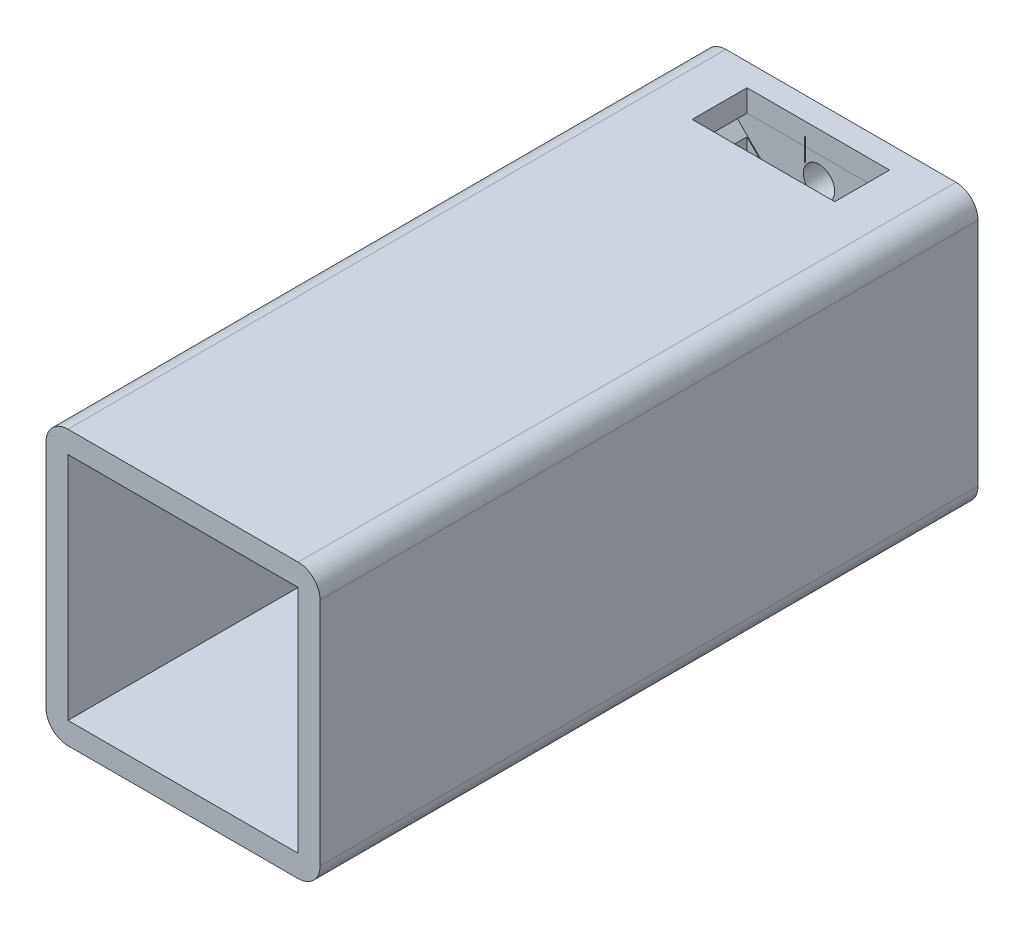
SolidWorks part; units mm, degrees
ref_plane "Front Plane" through (0, 0, 0) normal (0, 0, 1) x (1, 0, 0)
ref_plane "Top Plane" through (0, 0, 0) normal (0, 1, 0) x (1, 0, 0)
ref_plane "Right Plane" through (0, 0, 0) normal (1, 0, 0) x (0, 0, -1)
sketch "Sketch1" plane through (0, 0, 0) normal (0, 0, 1) x (1, 0, 0)
  line L1 (-12.5, -12.5) -> (12.5, -12.5)
  line L2 (-12.5, -12.5) -> (-12.5, 12.5)
  line L3 (-12.5, 12.5) -> (12.5, 12.5)
  line L4 (12.5, -12.5) -> (12.5, 12.5)
  line L5 (-12.5, -12.5) -> (12.5, 12.5) construction
  line L6 (-12.5, 12.5) -> (12.5, -12.5) construction
  point P0 (0, 0)
  dimension "D1" = 25
sketch "Sketch2" plane through (0, 0, 0) normal (0, 0, 1) x (1, 0, 0)
  line L5 (-12.5, -12.5) -> (12.5, 12.5) construction
  line L6 (-12.5, 12.5) -> (12.5, -12.5) construction
  circle A0 centre (0, 0) radius 2.5
  circle A1 centre (8.25, 0) radius 1.425
  circle A2 centre (0, -8.25) radius 1.425
  circle A3 centre (-8.25, 0) radius 1.425
  circle A4 centre (0, 8.25) radius 1.425
  point P0 (0, 0)
  dimension "D2" = 4
  dimension "D1" = 25
extrude "Boss-Extrude1" add sketch "Sketch1" along normal blind 60
shell "Shell1" thickness 2
extrude "Cut-Extrude4" cut sketch "Sketch2" along normal blind 2
sketch "Sketch4" plane through (0, 0, 2) normal (0, 0, 1) x (1, 0, 0)
  line L0 (0, 0) -> (-8.2, 0)
  line L1 (-5.7033, -6) -> (4.2967, -6)
  line L3 (-5.7033, 6) -> (4.2967, 6)
  line L5 (-5.7033, -6) -> (4.2967, 6) construction
  line L6 (-5.7033, 6) -> (4.2967, -6) construction
  line L7 (0, 0) -> (8.2, 0)
  line L8 (0, 0) -> (0, 6)
  line L9 (0, 0) -> (0, -6)
  line L11 (-10.5, 8.3787) -> (8.3787, -10.5)
  line L12 (-10.5, -10.5) -> (10.5, -10.5) construction
  line L13 (-8.3787, 10.5) -> (10.5, -8.3787)
  line L14 (10.5, -10.5) -> (10.5, 10.5) construction
  line L15 (-10.5, -8.3787) -> (8.3787, 10.5)
  line L16 (10.5, 10.5) -> (-10.5, 10.5) construction
  line L17 (-8.3787, -10.5) -> (10.5, 8.3787)
  line L19 (-9.5, -6.75) -> (9.5, -6.75)
  line L20 (-9.5, -6.75) -> (-9.5, 6.75)
  line L21 (-9.5, 6.75) -> (9.5, 6.75)
  line L22 (9.5, -6.75) -> (9.5, 6.75)
  line L23 (-9.5, -6.75) -> (9.5, 6.75) construction
  line L24 (-9.5, 6.75) -> (9.5, -6.75) construction
  arc A2 (-5.7033, -6) -> (-5.7033, 6) centre (0.2578, 0) cw
  arc A3 (4.2967, 6) -> (4.2967, -6) centre (1.6369, 0) cw
  point P0 (0, 0)
  point P12 (0, 0)
  point P22 (0, 0)
  point P25 (0, 0)
  point P28 (0, 0)
  point P33 (-1.0607, -1.0607)
  point P38 (1.0607, 1.0607)
  point P43 (-1.0607, 1.0607)
  point P46 (1.0607, -1.0607)
  circle M9 centre (8.25, 0) radius 1.425
  circle M11 centre (-8.25, 0) radius 1.425
  line M13 (10.5, -10.5) -> (10.5, 10.5)
  line M14 (10.5, 10.5) -> (-10.5, 10.5)
  line M15 (-10.5, 10.5) -> (-10.5, -10.5)
  line M16 (-10.5, -10.5) -> (10.5, -10.5)
  dimension "D1" = 19
extrude "Boss-Extrude3" add sketch "Sketch4" along normal blind 30 contours L11 A2 L3 L13 L21 | L11 L21 L13 M14 M15 | L21 L13 L3 L15 | L15 L21 L17 M13 M14 | L3 A3 L17 L21 L15 | L1 A2 L15 L19 L17 | L13 A3 L1 L11 L19 | L19 L15 L17 M15 M16 | L19 L11 L13 M16 M13 | L17 A3 L22 L21 M9 | A3 L13 L19 L22 M9 | L17 L19 L11 L1 | L15 A2 L20 L19 M11 | A2 L11 L21 L20 M11 | A2 L20 M11 | A3 L22 M9
sketch "Sketch5" plane through (0, 12.5, 0) normal (0, 1, 0) x (1, 0, 0)
  line L0 (0, 0) -> (0, -4.5668)
  line L2 (-6.5, -7.0668) -> (6.5, -7.0668)
  line L3 (-6.5, -7.0668) -> (-6.5, -2.0668)
  line L4 (-6.5, -2.0668) -> (6.5, -2.0668)
  line L5 (6.5, -7.0668) -> (6.5, -2.0668)
  line L6 (-6.5, -7.0668) -> (6.5, -2.0668) construction
  line L7 (-6.5, -2.0668) -> (6.5, -7.0668) construction
  circle A0 centre (0.0246, -3.3013) radius 0.0246
  point P3 (0.0246, -4.5668)
  dimension "D1" = 13
  dimension "D2" = 5
fillet "Fillet1" radius 2 4 edges at (-12.5, -12.5, 30) (12.5, 12.5, 30) (12.5, -12.5, 30) (-12.5, 12.5, 30)
extrude "Cut-Extrude6" cut sketch "Sketch5" against normal blind 10
